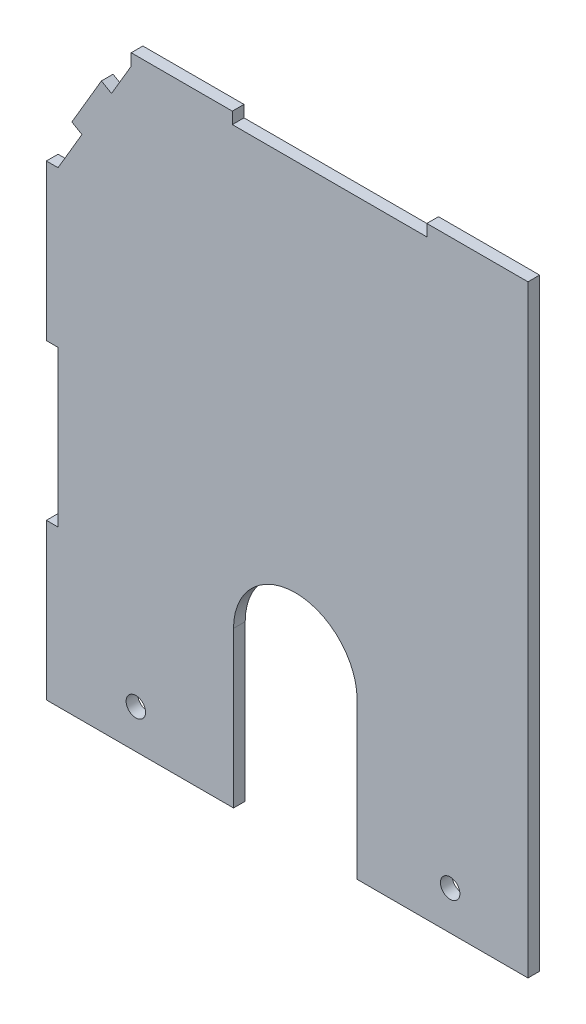
SolidWorks part; units mm, degrees
ref_plane "Front Plane" through (0, 0, 0) normal (0, 0, 1) x (1, 0, 0)
ref_plane "Top Plane" through (0, 0, 0) normal (0, 1, 0) x (1, 0, 0)
ref_plane "Right Plane" through (0, 0, 0) normal (1, 0, 0) x (0, 0, -1)
sketch "Sketch1" plane through (0, 0, 0) normal (0, 0, 1) x (1, 0, 0)
  line L1 (34.37, 75.956) -> (-15.63, 75.956)
  line L2 (60.37, 75.956) -> (60.37, -76.044)
  line L3 (60.37, -76.044) -> (16.4443, -76.044)
  line L4 (-60.44, 3.956) -> (-60.44, -36.044)
  line L5 (60.37, 75.956) -> (-60.44, -76.044) construction
  line L6 (60.37, -76.044) -> (0, 0) construction
  line L7 (-15.3243, -36.044) -> (-15.3243, -76.044)
  line L8 (16.4443, -36.044) -> (16.4443, -76.044)
  line L9 (-15.3243, -76.044) -> (-60.44, -76.044)
  line L10 (-41.63, 75.956) -> (-41.63, 78.956)
  line L11 (-41.63, 78.956) -> (-15.63, 78.956)
  line L12 (-15.63, 78.956) -> (-15.63, 75.956)
  line L13 (60.37, 75.956) -> (60.37, 78.956)
  line L14 (60.37, 78.956) -> (34.37, 78.956)
  line L15 (34.37, 78.956) -> (34.37, 75.956)
  line L16 (-60.44, 43.956) -> (-63.44, 43.956)
  line L17 (-63.44, 43.956) -> (-63.44, 3.956)
  line L18 (-63.44, 3.956) -> (-60.44, 3.956)
  line L19 (-60.44, -76.044) -> (-63.44, -76.044)
  line L20 (-63.44, -76.044) -> (-63.44, -36.044)
  line L21 (-63.44, -36.044) -> (-60.44, -36.044)
  line L29 (-41.63, 75.956) -> (-46.6975, 67.335)
  line L31 (-54.2987, 54.4036) -> (-56.885, 55.9239)
  line L32 (-46.6975, 67.335) -> (-49.2838, 68.8553)
  line L33 (-56.885, 55.9239) -> (-49.2838, 68.8553)
  line L34 (-54.2987, 54.4036) -> (-60.44, 43.956)
  circle A0 centre (-40.44, -66.044) radius 2.5
  circle A1 centre (40.37, -66.044) radius 2.5
  arc A2 (16.4443, -36.044) -> (-15.3243, -36.044) centre (0.56, -36.044) ccw
  point P0 (0, 0)
  dimension "D6" = 5
  dimension "D7" = 20
  dimension "D8" = 10
  dimension "D9" = 5
  dimension "D10" = 10
  dimension "D11" = 20
  dimension "D12" = 40
  dimension "D13" = 61
  dimension "D1" = 120.81
  dimension "D2" = 152
  dimension "D3" = 102
  dimension "D4" = 120
  dimension "D5" = 60.44
  dimension "D14" = 50
  dimension "D15" = 26
  dimension "D16" = 3
  dimension "D17" = 3
  dimension "D18" = 40
  dimension "D19" = 40
  dimension "D20" = 3
  dimension "D21" = 3
  dimension "D22" = 10
  dimension "D23" = 15
  dimension "D24" = 3
extrude "Boss-Extrude1" add sketch "Sketch1" along normal blind 3
